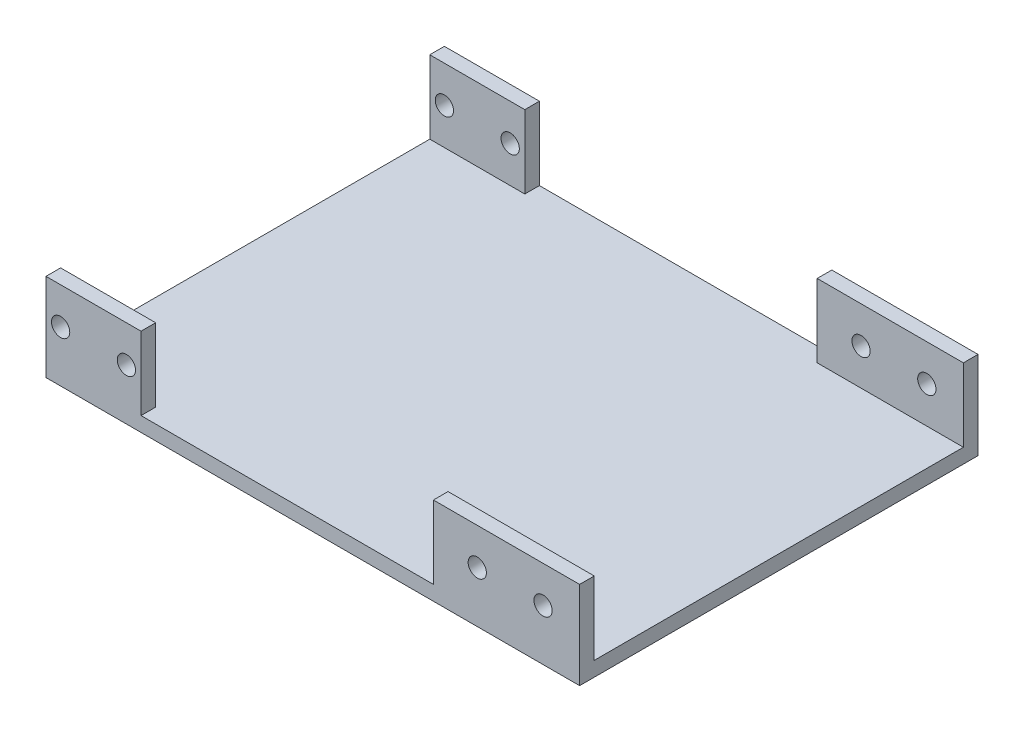
SolidWorks part; units mm, degrees
ref_plane "Front Plane" through (0, 0, 0) normal (0, 0, 1) x (1, 0, 0)
ref_plane "Top Plane" through (0, 0, 0) normal (0, 1, 0) x (1, 0, 0)
ref_plane "Right Plane" through (0, 0, 0) normal (1, 0, 0) x (0, 0, -1)
sketch "Sketch1" plane through (0, 0, 0) normal (0, 1, 0) x (1, 0, 0)
  line L1 (-51.9985, 29.194) -> (21.0015, 29.194)
  line L2 (-51.9985, 29.194) -> (-51.9985, -25.306)
  line L3 (-51.9985, -25.306) -> (21.0015, -25.306)
  line L4 (21.0015, 29.194) -> (21.0015, -25.306)
  dimension "D1" = 73
  dimension "D2" = 54.5
extrude "Boss-Extrude1" add sketch "Sketch1" along normal blind 2
sketch "Sketch2" plane through (0, 2, 0) normal (0, 1, 0) x (1, 0, 0)
  line L0 (21.0015, 29.194) -> (-51.9985, 29.194) construction
  line L1 (1.0015, 29.194) -> (21.0015, 29.194)
  line L2 (1.0015, 29.194) -> (1.0015, 27.194)
  line L3 (1.0015, 27.194) -> (21.0015, 27.194)
  line L4 (21.0015, 29.194) -> (21.0015, 27.194)
  line L5 (1.0015, -23.306) -> (21.0015, -23.306)
  line L6 (1.0015, -23.306) -> (1.0015, -25.306)
  line L7 (1.0015, -25.306) -> (21.0015, -25.306)
  line L8 (21.0015, -23.306) -> (21.0015, -25.306)
  line L9 (-51.9985, -25.306) -> (21.0015, -25.306) construction
  line L10 (21.0015, -25.306) -> (21.0015, 29.194) construction
  line L11 (-51.9985, 29.194) -> (-51.9985, -25.306) construction
  line L16 (-51.9985, 29.194) -> (-38.9985, 29.194)
  line L17 (-51.9985, 29.194) -> (-51.9985, 27.194)
  line L18 (-51.9985, 27.194) -> (-38.9985, 27.194)
  line L19 (-38.9985, 29.194) -> (-38.9985, 27.194)
  line L20 (-51.9985, -23.306) -> (-38.9985, -23.306)
  line L21 (-51.9985, -23.306) -> (-51.9985, -25.306)
  line L22 (-51.9985, -25.306) -> (-38.9985, -25.306)
  line L23 (-38.9985, -23.306) -> (-38.9985, -25.306)
  dimension "D1" = 20
  dimension "D2" = 2
  dimension "D3" = 20
  dimension "D4" = 2
  dimension "D5" = 0
  dimension "D6" = 0
  dimension "D7" = 0
  dimension "D8" = 0
  dimension "D9" = 2
  dimension "D10" = 2
  dimension "D11" = 60
  dimension "D12" = 60
  dimension "D13" = 0
  dimension "D14" = 0
  dimension "D15" = 0
  dimension "D16" = 0
extrude "Boss-Extrude2" add sketch "Sketch2" along normal blind 10
sketch "Sketch3" plane through (0, 0, 25.306) normal (0, 0, 1) x (1, 0, 0)
  line L1 (21.0015, 12) -> (21.0015, 0) construction
  line L2 (-38.9985, 2) -> (1.0015, 2) construction
  circle A0 centre (16.0015, 7) radius 1.25
  circle A1 centre (7.0015, 7) radius 1.25
  circle A2 centre (-40.9985, 7) radius 1.25
  circle A3 centre (-49.9985, 7) radius 1.25
  dimension "D1" = 2.5
  dimension "D2" = 2.5
  dimension "D3" = 2.5
  dimension "D4" = 2.5
  dimension "D5" = 5
  dimension "D6" = 5
  dimension "D7" = 9
  dimension "D8" = 5
  dimension "D9" = 5
  dimension "D10" = 5
  dimension "D11" = 9
  dimension "D12" = 48
extrude "Cut-Extrude1" cut sketch "Sketch3" against normal through all
